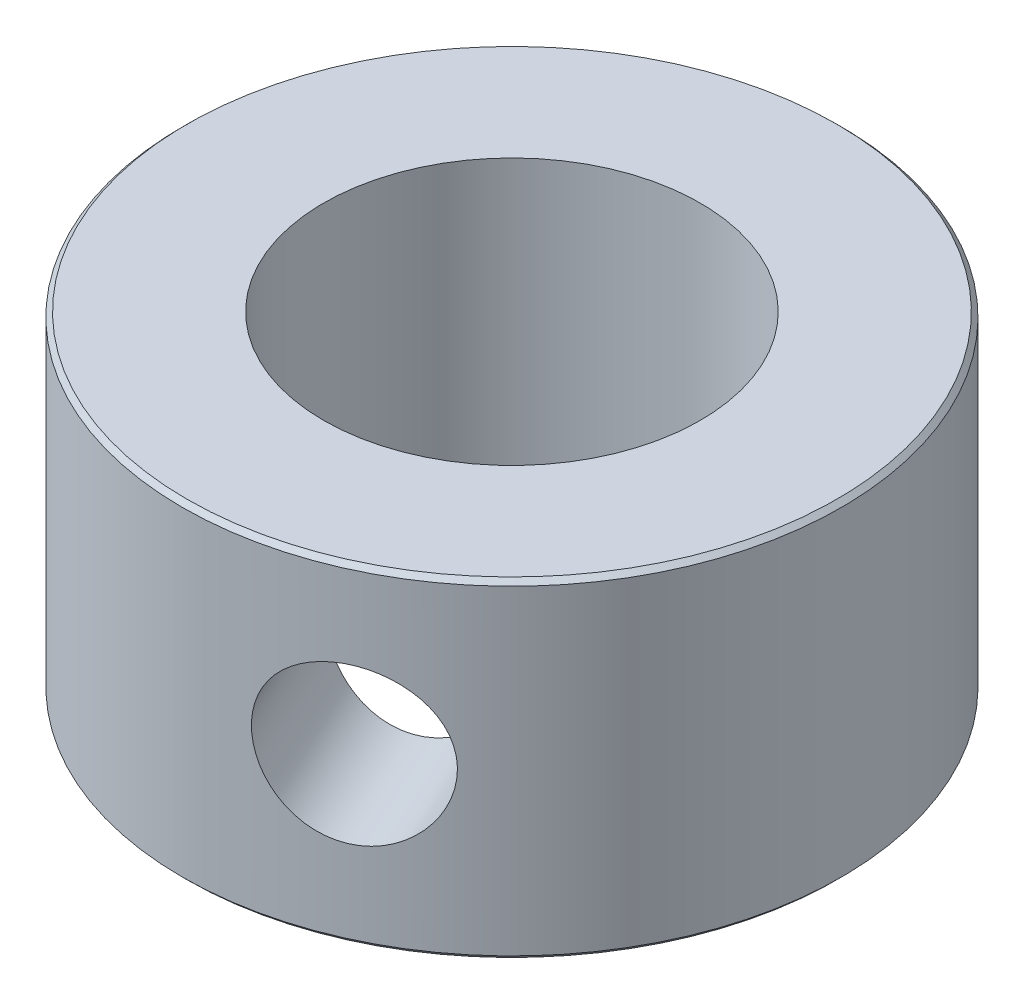
SolidWorks part; units mm, degrees
ref_plane "Front Plane" through (0, 0, 0) normal (0, 0, 1) x (1, 0, 0)
ref_plane "Top Plane" through (0, 0, 0) normal (0, 1, 0) x (1, 0, 0)
ref_plane "Right Plane" through (0, 0, 0) normal (1, 0, 0) x (0, 0, -1)
sketch "Sketch2" plane through (0, 0, 0) normal (0, 1, 0) x (1, 0, 0)
  circle A0 centre (0, 0) radius 4
  circle A1 centre (0, 0) radius 7
extrude "Boss-Extrude1" add sketch "Sketch2" along normal blind 7
hole_wizard "M4x0.7 Tapped Hole1" positions "3DSketch4" profile "Sketch7" tap size "M4x0.7" standard "ANSI Metric"
sketch3d "3DSketch4"
  point P0 (2.9196, 3.5, 6.3621)
  dimension "D1" = 3.5
sketch "Sketch7" plane through (2.9196, 3.5, 6.3621) normal (0, 1, 0) x (0.9089, 0, -0.4171)
  line L0 (0, 0) -> (0, 4.9914)
  line L1 (0, 4.9914) -> (1.65, 4)
  line L2 (1.65, 4) -> (1.65, 0)
  line L5 (1.65, 0) -> (0, 0)
  line L10 (0, 4.9914) -> (-1.65, 4) construction
  line L11 (0, -6.35) -> (0, 107.95) construction
  dimension "Tap Drill Dia." = 3.3
  dimension "Tap Drill Depth" = 4
  dimension "Drill Angle" = 118
cosmetic thread "Hole Thread1" parameters "D1"=8, "D2"=4
chamfer "Chamfer1" distance 0.1 angle 45 2 edges at (0, 0, 7) (0, 7, 7)
